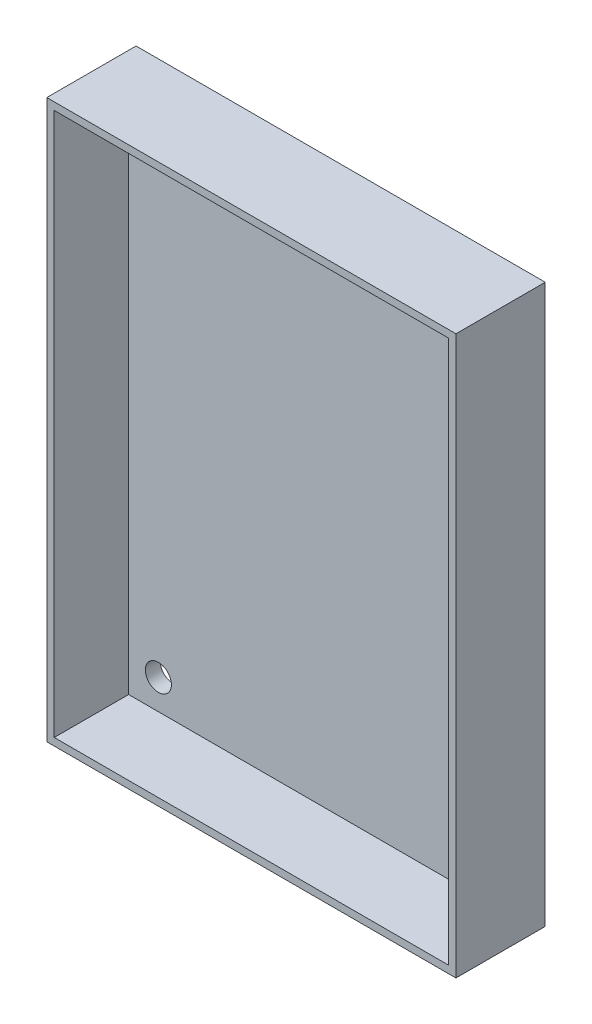
SolidWorks part; units mm, degrees
material "PA Тип 6"
ref_plane "Спереди" through (0, 0, 0) normal (0, 0, 1) x (1, 0, 0)
ref_plane "Сверху" through (0, 0, 0) normal (0, 1, 0) x (1, 0, 0)
ref_plane "Справа" through (0, 0, 0) normal (1, 0, 0) x (0, 0, -1)
sketch "Эскиз1" plane through (0, 0, 0) normal (0, 0, 1) x (1, 0, 0)
  line L1 (0, 0) -> (55, 0)
  line L2 (0, 0) -> (0, 75)
  line L3 (0, 75) -> (55, 75)
  line L4 (55, 0) -> (55, 75)
  circle A0 centre (5, 70) radius 1.75
  circle A1 centre (50, 70) radius 1.75
  circle A2 centre (5, 5) radius 1.75
  circle A3 centre (50, 5) radius 1.75
  dimension "D3" = 3.5
  dimension "D4" = 3.5
  dimension "D5" = 5
  dimension "D6" = 5
  dimension "D7" = 5
  dimension "D8" = 5
  dimension "D9" = 3.5
  dimension "D10" = 5
  dimension "D11" = 5
  dimension "D12" = 3.5
  dimension "D13" = 5
  dimension "D14" = 5
  dimension "D1" = 55
  dimension "D2" = 75
extrude "Бобышка-Вытянуть1" add sketch "Эскиз1" along normal blind 2
sketch "Эскиз2" plane through (0, 0, 2) normal (0, 0, 1) x (1, 0, 0)
  line L1 (0, 75) -> (55, 75)
  line L2 (0, 75) -> (0, 0)
  line L3 (0, 0) -> (55, 0)
  line L4 (55, 75) -> (55, 0)
  line L5 (1, 74) -> (54, 74)
  line L6 (1, 74) -> (1, 1)
  line L7 (1, 1) -> (54, 1)
  line L8 (54, 74) -> (54, 1)
  dimension "D1" = 1
  dimension "D2" = 1
  dimension "D3" = 1
  dimension "D4" = 1
extrude "Бобышка-Вытянуть2" add sketch "Эскиз2" along normal blind 10
